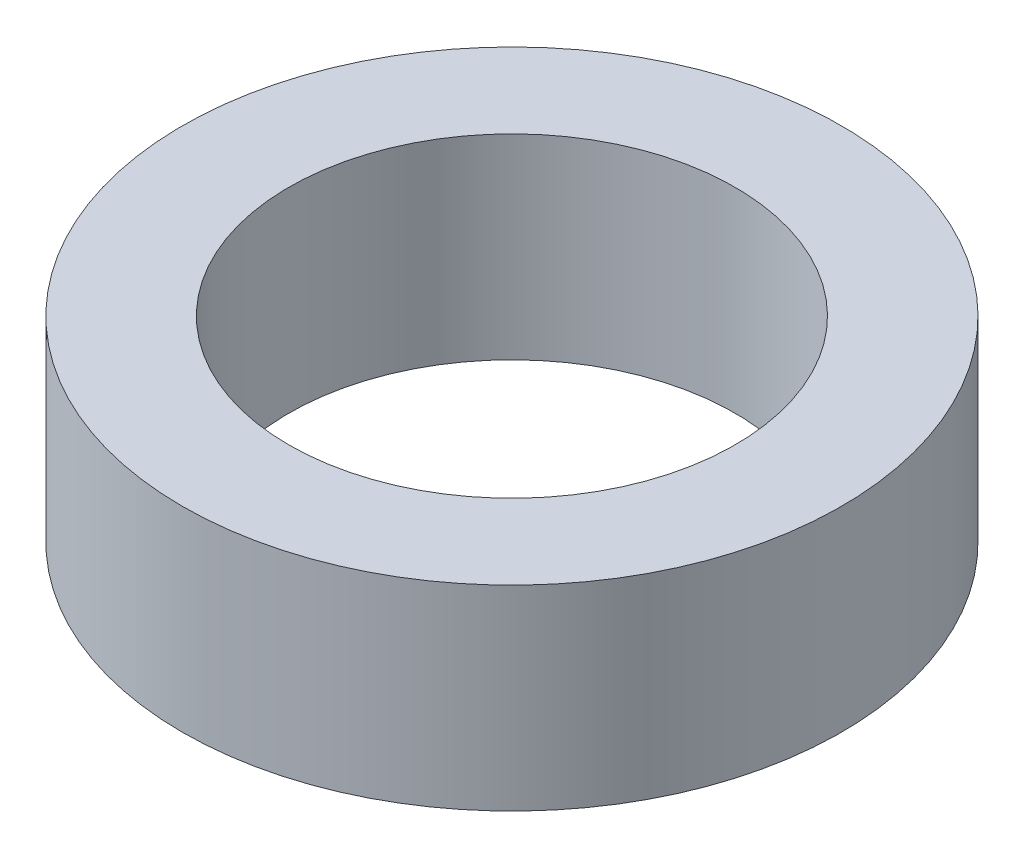
SolidWorks part; units mm, degrees
ref_plane "Front Plane" through (0, 0, 0) normal (0, 0, 1) x (1, 0, 0)
ref_plane "Top Plane" through (0, 0, 0) normal (0, 1, 0) x (1, 0, 0)
ref_plane "Right Plane" through (0, 0, 0) normal (1, 0, 0) x (0, 0, -1)
sketch "Sketch1" plane through (0, 0, 0) normal (0, 1, 0) x (1, 0, 0)
  circle A0 centre (0, 0) radius 9.6
  circle A1 centre (0, 0) radius 6.5
  dimension "D1" = 13
  dimension "D2" = 19.2
extrude "Boss-Extrude1" add sketch "Sketch1" along normal blind 5.7
